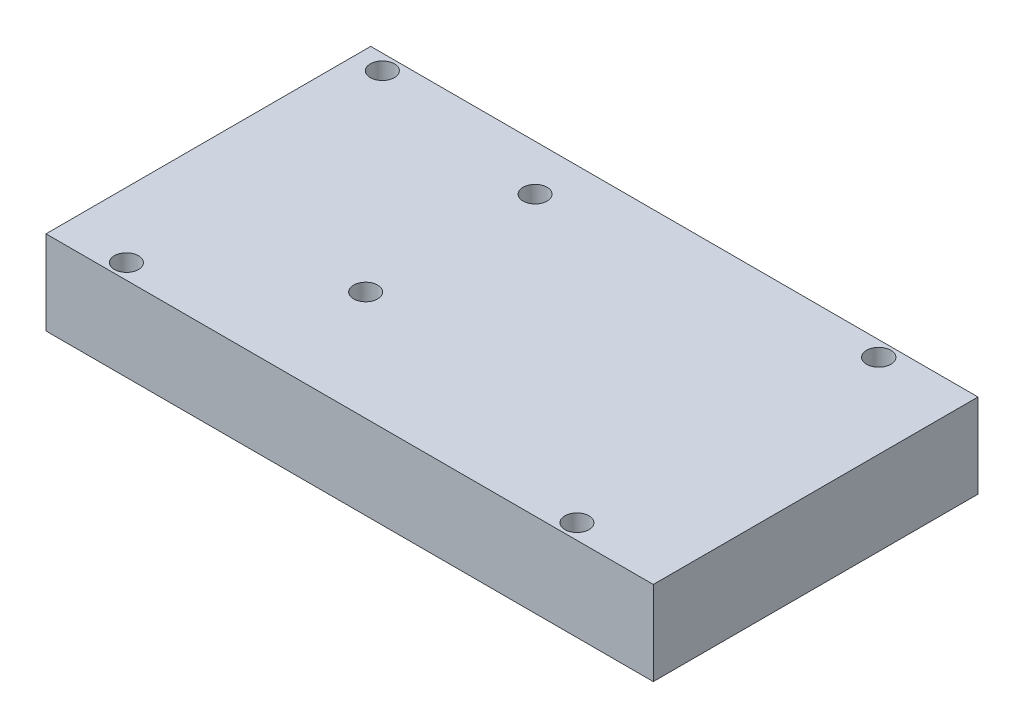
SolidWorks part; units mm, degrees
ref_plane "Płaszczyzna przednia" through (0, 0, 0) normal (0, 0, 1) x (1, 0, 0)
ref_plane "Płaszczyzna górna" through (0, 0, 0) normal (0, 1, 0) x (1, 0, 0)
ref_plane "Płaszczyzna prawa" through (0, 0, 0) normal (1, 0, 0) x (0, 0, -1)
sketch "Sketch1" plane through (0, 0, 0) normal (0, 1, 0) x (1, 0, 0)
  line L1 (-50.5, -27) -> (50.5, -27)
  line L2 (-50.5, -27) -> (-50.5, 27)
  line L3 (-50.5, 27) -> (50.5, 27)
  line L4 (50.5, -27) -> (50.5, 27)
  line L5 (-50.5, -27) -> (50.5, 27) construction
  line L6 (-50.5, 27) -> (50.5, -27) construction
  point P0 (0, 0)
  dimension "D1" = 101
  dimension "D2" = 54
extrude "Boss-Extrude1" add sketch "Sketch1" along normal blind 14
sketch "Sketch2" plane through (0, 14, 0) normal (0, 1, 0) x (1, 0, 0)
  line L0 (50.5, -27) -> (50.5, 27) construction
  line L1 (-50.5, -27) -> (50.5, -27) construction
  line L2 (50.5, 27) -> (-50.5, 27) construction
  circle A0 centre (-46.02, 24.46) radius 2
  circle A1 centre (-39.67, -24.46) radius 2
  circle A2 centre (36.53, 24.46) radius 2.0233
  circle A3 centre (35.26, -24.46) radius 2
  circle A4 centre (-15.54, 19.38) radius 2
  circle A5 centre (-15.54, -8.7989) radius 2
  dimension "D1" = 13.97
  dimension "D9" = 66.04
  dimension "D2" = 15.24
  dimension "D3" = 2.54
  dimension "D4" = 2.54
  dimension "D5" = 96.52
  dimension "D6" = 90.17
  dimension "D7" = 2.54
  dimension "D8" = 2.54
  dimension "D10" = 66.04
  dimension "D11" = 7.62
  dimension "D12" = 18.2011
extrude "Cut-Extrude1" cut sketch "Sketch2" against normal blind 100
